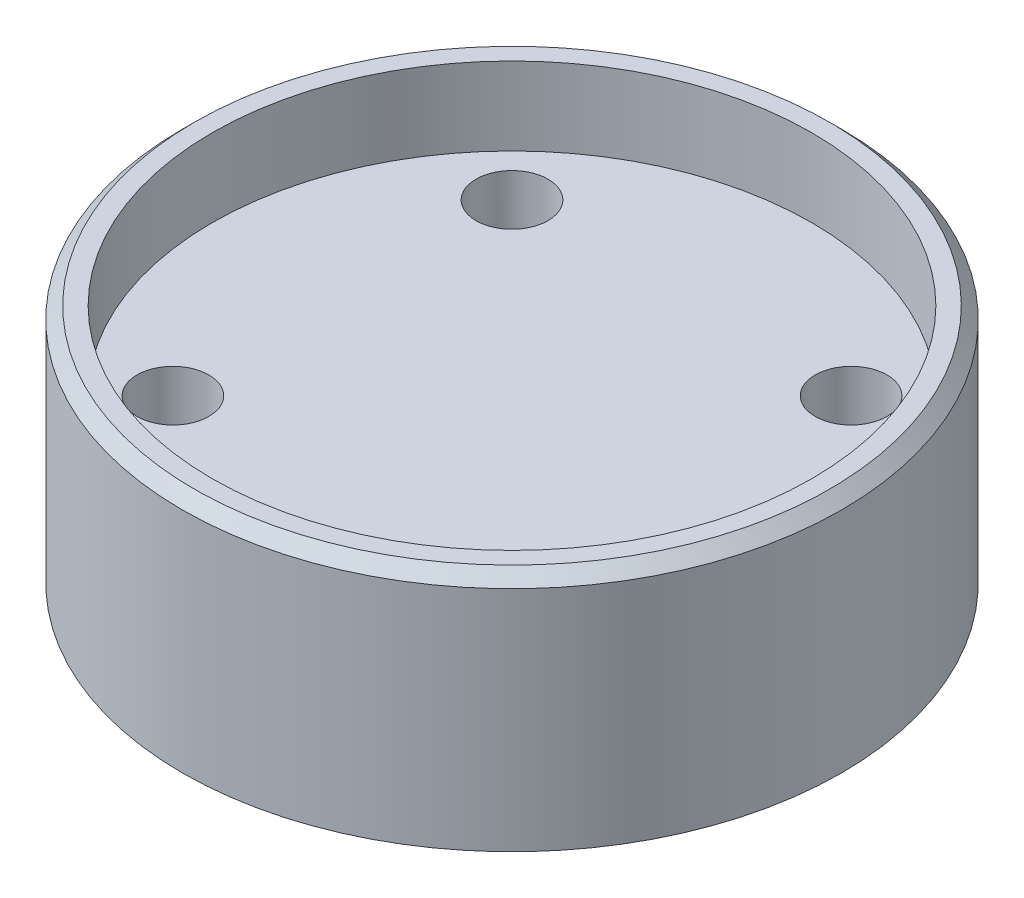
SolidWorks part; units mm, degrees
material "Polybutadiene (PB)"
ref_plane "Front Plane" through (0, 0, 0) normal (0, 0, 1) x (1, 0, 0)
ref_plane "Top Plane" through (0, 0, 0) normal (0, 1, 0) x (1, 0, 0)
ref_plane "Right Plane" through (0, 0, 0) normal (1, 0, 0) x (0, 0, -1)
sketch "Sketch1" plane through (0, 0, 0) normal (0, 0, 1) x (1, 0, 0)
  line L0 (0, -626.6874) -> (0, 30707.6802) construction
  line L1 (-626.6874, 0) -> (30707.6802, 0) construction
  line L3 (27.5, 0) -> (27.5, 20)
  line L4 (27.5, 20) -> (25, 20)
  line L5 (25, 20) -> (25, 13.5)
  line L6 (25, 13.5) -> (0, 13.5)
  line L10 (27.5, 0) -> (0, 0)
  line L13 (0, 13.5) -> (0, 0)
  point P4 (0, 0)
  point P7 (0, 0.4631)
  point P12 (0, 13.5)
  point P15 (0, 13.836)
  dimension "D1" = 55
  dimension "D2" = 50
  dimension "D3" = 6.5
  dimension "D5" = 20
revolve "Revolve1" add sketch "Sketch1" angle 360 about L0
sketch "Sketch2" plane through (0, 0, 0) normal (0, 1, 0) x (1, 0, 0)
  line L0 (0, -1000) -> (0, 49000) construction
  line L1 (-14.1421, -14.1421) -> (14.1421, -14.1421) construction
  line L2 (-14.1421, -14.1421) -> (-14.1421, 14.1421) construction
  line L3 (-14.1421, 14.1421) -> (14.1421, 14.1421) construction
  line L4 (14.1421, -14.1421) -> (14.1421, 14.1421) construction
  line L5 (-14.1421, -14.1421) -> (14.1421, 14.1421) construction
  line L6 (-14.1421, 14.1421) -> (14.1421, -14.1421) construction
  line L7 (-1000, 0) -> (49000, 0) construction
  circle A0 centre (-14.1421, 14.1421) radius 3
  circle A1 centre (14.1421, 14.1421) radius 3
  circle A2 centre (14.1421, -14.1421) radius 3
  circle A3 centre (-14.1421, -14.1421) radius 3
  point P0 (0, 0)
  dimension "D2" = 6
  dimension "D1" = 40
extrude "Cut-Extrude2" cut sketch "Sketch2" against normal through all and the other way through all
chamfer "Chamfer1" distance 1 angle 45 1 edges at (27.5, 20, 0)
